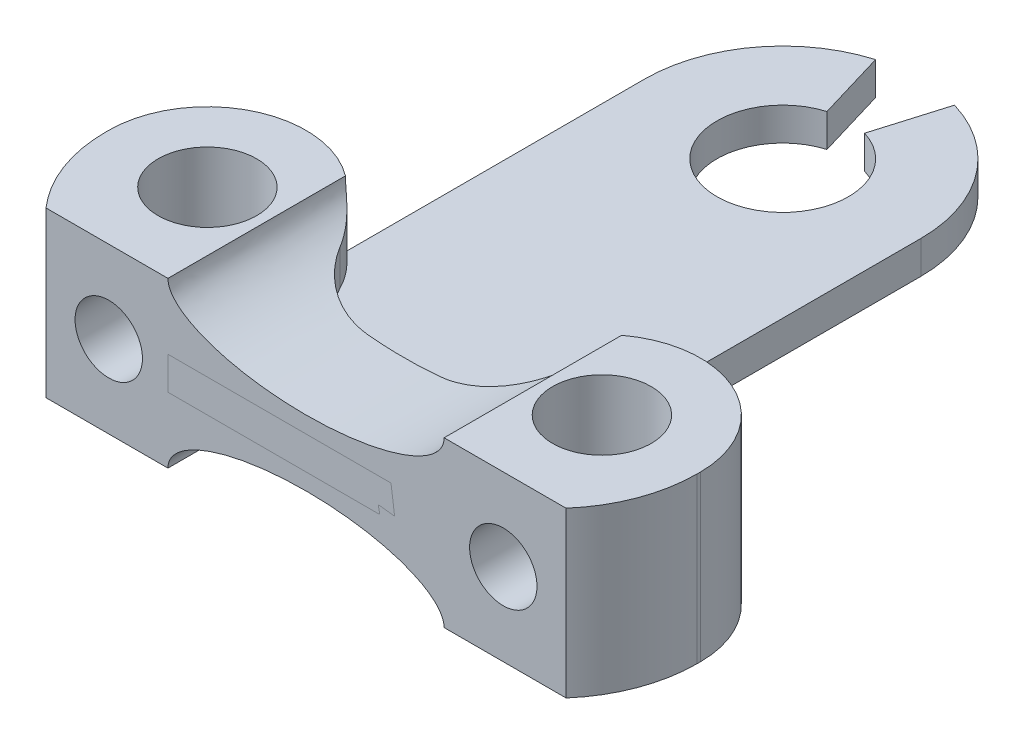
SolidWorks part; units mm, degrees
ref_plane "Front Plane" through (0, 0, 0) normal (0, 0, 1) x (1, 0, 0)
ref_plane "Top Plane" through (0, 0, 0) normal (0, 1, 0) x (1, 0, 0)
ref_plane "Right Plane" through (0, 0, 0) normal (1, 0, 0) x (0, 0, -1)
sketch "Sketch2" plane through (0, 0, 0) normal (0, 1, 0) x (1, 0, 0)
  line L0 (-0.5714, 19.1133) -> (-1.2, 21.2216)
  line L2 (1.2, 21.2216) -> (0.5714, 19.1133)
  line L4 (-4.2, 17.1966) -> (-4.2, 1.1966)
  line L5 (4.2, 17.1966) -> (4.2, 1.1966)
  line L6 (-4.2, 1.1966) -> (4.2, 1.1966)
  arc A0 (-1.2, 21.2216) -> (-4.2, 17.1966) centre (0, 17.1966) ccw
  arc A1 (-0.5714, 19.1133) -> (0.5714, 19.1133) centre (0, 17.1966) ccw
  arc A2 (4.2, 17.1966) -> (1.2, 21.2216) centre (0, 17.1966) ccw
  dimension "D1" = 4
  dimension "D2" = 8.4
  dimension "D3" = 2.4
  dimension "D4" = 16
extrude "Boss-Extrude1" add sketch "Sketch2" along normal blind 1
sketch "Sketch3" plane through (0, 0, 0) normal (0, -1, 0) x (1, 0, 0)
  line L0 (4.6, -1.1966) -> (-4.6, -1.1966)
  line L1 (9, -5.5966) -> (9, -5.6966)
  line L2 (-9, -5.5966) -> (-9, -5.6966)
  line L3 (9, -8.6966) -> (9.3541, -8.6966)
  line L4 (-4.2, -1.1966) -> (4.2, -1.1966) construction
  line L5 (-4.5, -5.6966) -> (4.5, -5.6966) construction
  line L6 (-9, -9.0507) -> (-9, -8.6966)
  line L7 (-9.3541, -8.6966) -> (-9, -8.6966)
  line L8 (6, -8.6966) -> (-6, -8.6966)
  line L9 (9, -9.0507) -> (9, -8.6966)
  line L10 (-1.101, -5.6966) -> (1.101, -5.6966)
  line L11 (-9, -5.6966) -> (-9, -9.0507)
  line L12 (-9.3541, -8.6966) -> (-6, -8.6966)
  circle A0 centre (-6, -5.6966) radius 1.5
  circle A1 centre (6, -5.6966) radius 1.5
  arc A2 (-9, -5.6966) -> (-6, -8.6966) centre (-6, -5.6966) ccw
  arc A3 (-6, -8.6966) -> (-3.3278, -7.0603) centre (-6, -5.6966) ccw
  circle A5 centre (0, -17.1966) radius 2
  arc A6 (9, -5.5966) -> (4.6, -1.1966) centre (4.6, -5.5966) ccw
  arc A7 (3.3278, -7.0603) -> (6, -8.6966) centre (6, -5.6966) ccw
  arc A8 (6, -8.6966) -> (9, -5.6966) centre (6, -5.6966) ccw
  arc A10 (-4.6, -1.1966) -> (-9, -5.5966) centre (-4.6, -5.5966) ccw
  arc A11 (3.3278, -7.0603) -> (1.101, -5.6966) centre (1.101, -8.1966) ccw
  arc A12 (-3.3278, -7.0603) -> (-1.101, -5.6966) centre (-1.101, -8.1966) cw
  point P0 (0, -1.1966)
  point P14 (0, -5.6966)
  point P31 (9, -1.1966)
  point P36 (3, -5.6966)
  point P39 (-3, -5.6966)
  dimension "D3" = 11.5
  dimension "D4" = 2.5
  dimension "D6" = 4.4
  dimension "D1" = 18
  dimension "D2" = 7.5
  dimension "D5" = 12
extrude "Boss-Extrude2" add sketch "Sketch3" along normal blind 5 from offset 3 separate body offset against normal yes
sketch "Sketch4" plane through (0, 0, -1.1966) normal (0, 0, 1) x (1, 0, 0)
  line L2 (-6, 3) -> (-6, 0.5) construction
  line L4 (-6, 0.5) -> (-6, -2) construction
  line L6 (6, 3) -> (6, 0.5) construction
  line L7 (6, 0.5) -> (6, -2) construction
  line L8 (6, 0.5) -> (0, 0.5) construction
  line L10 (0, 0.5) -> (-6, 0.5) construction
  line L11 (-4.6, 3) -> (-9, 3) construction
  line L13 (9, 3) -> (4.6, 3) construction
  line L14 (-9, -2) -> (-4.6, -2) construction
  line L15 (4.6, -2) -> (9, -2) construction
  circle A0 centre (-6, 0.5) radius 1.025
  circle A1 centre (6, 0.5) radius 1.025
  point P6 (0, 0)
  point P10 (0, 0)
  point P12 (0, 0)
  point P16 (0, 0)
  point P19 (0, 0)
  dimension "D1" = 12
extrude "Cut-Extrude1" cut sketch "Sketch4" against normal up to next
sketch "Sketch5" plane through (0, 0, -5.6966) normal (0, 0, -1) x (-1, 0, 0)
  line L1 (9, 3) -> (3.3278, 3) construction
  line L2 (2, 1) -> (-2, 1) construction
  line L3 (-4.2, 3) -> (4.2, 3)
  line L5 (-4.2, 3) -> (-4.2, 0.5)
  line L6 (4.2, 3) -> (4.2, 0.5)
  line L7 (-4.2, 1) -> (-4.2, 0) construction
  line L8 (4.2, 1) -> (4.2, 0) construction
  line L10 (3.3278, -2) -> (9, -2) construction
  line L11 (-2, 0) -> (2, 0) construction
  line L12 (-4.2, -2) -> (-4.2, 0.5)
  line L13 (4.2, -2) -> (4.2, 0.5)
  line L14 (-4.6, -2) -> (4.6, -2) construction
  line L15 (-4.6, 3) -> (4.6, 3) construction
  ellipse E0 centre (0, 3) end of major axis (-4.2, 3) minor radius 1.5
  ellipse E1 centre (0, -2) end of major axis (4.2, -2) minor radius 1.5
  point P8 (0, 0)
  point P31 (0, 0)
  dimension "D1" = 0.5
  dimension "D2" = 0.5
extrude "Cut-Extrude2" cut sketch "Sketch5" against normal through all both and the other way through all
sketch "Sketch6" plane through (0, -2, 0) normal (0, -1, 0) x (1, 0, 0)
  line L0 (-9, -5.5966) -> (-9, -5.6966) construction
  line L1 (-9, -2.6966) -> (9, -2.6966)
  line L2 (-9, -2.6966) -> (-9, -1.1966)
  line L3 (-9, -1.1966) -> (9, -1.1966)
  line L4 (9, -2.6966) -> (9, -1.1966)
  line L6 (9, -5.5966) -> (9, -5.6966) construction
  line L7 (4.2, -1.1966) -> (-4.2, -1.1966) construction
  circle A0 centre (-6, -5.6966) radius 1.5 construction
  point P6 (0, -1.1966)
  dimension "D1" = 3
extrude "Cut-Extrude3" cut sketch "Sketch6" against normal blind 5
